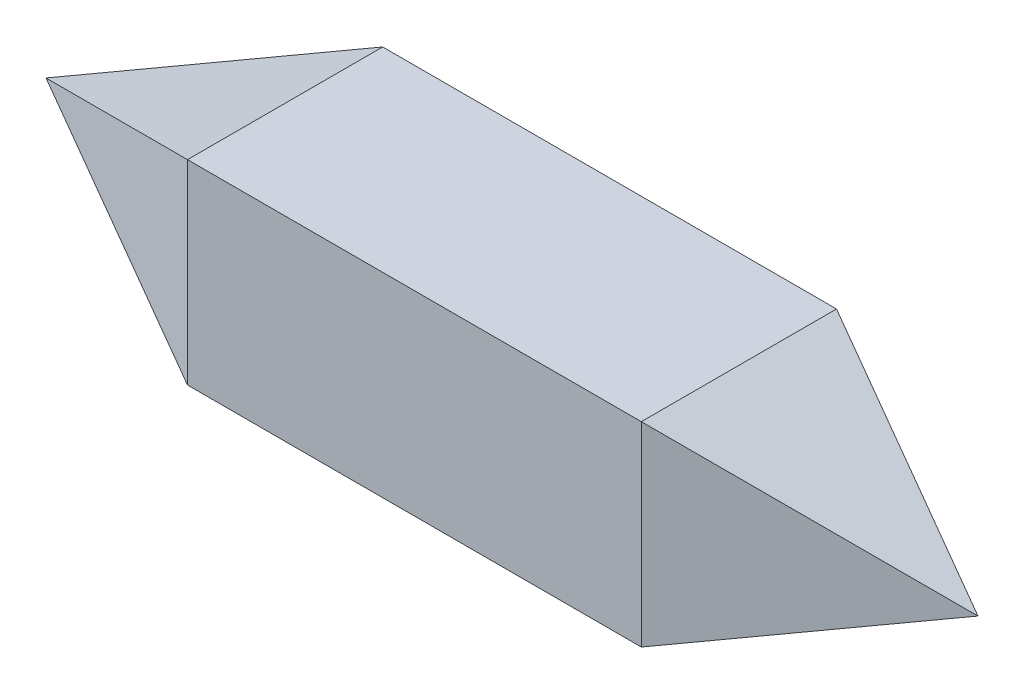
SolidWorks part; units mm, degrees
material "PET"
ref_plane "Plan de face" through (0, 0, 0) normal (0, 0, 1) x (1, 0, 0)
ref_plane "Plan de dessus" through (0, 0, 0) normal (0, 1, 0) x (1, 0, 0)
ref_plane "Plan de droite" through (0, 0, 0) normal (1, 0, 0) x (0, 0, -1)
sketch "Esquisse2" plane through (0, 0, 0) normal (0, 0, 1) x (1, 0, 0)
  line L1 (0, 0) -> (1000, 0)
  line L2 (0, 0) -> (0, 430.1)
  line L3 (0, 430.1) -> (1000, 430.1)
  line L4 (1000, 0) -> (1000, 430.1)
  dimension "D1" = 1000
  dimension "D2" = 430.1
extrude "Boss.-Extru.2" add sketch "Esquisse2" along normal blind 430.1
sketch "Esquisse7" plane through (0, 0, 0) normal (-1, 0, 0) x (0, 0, 1)
  line L1 (0, 0) -> (430.1, 0)
  line L2 (0, 0) -> (0, 430.1)
  line L3 (0, 430.1) -> (430.1, 430.1)
  line L4 (430.1, 0) -> (430.1, 430.1)
extrude "Boss.-Extru.5" add sketch "Esquisse7" along normal blind 1000 draft 22.206
sketch "Esquisse8" plane through (1000, 0, 0) normal (1, 0, 0) x (0, 0, -1)
  line L1 (0, 0) -> (-430.1, 0)
  line L2 (0, 0) -> (0, 430.1)
  line L3 (0, 430.1) -> (-430.1, 430.1)
  line L4 (-430.1, 0) -> (-430.1, 430.1)
extrude "Boss.-Extru.6" add sketch "Esquisse8" along normal blind 1000 draft 22.206
